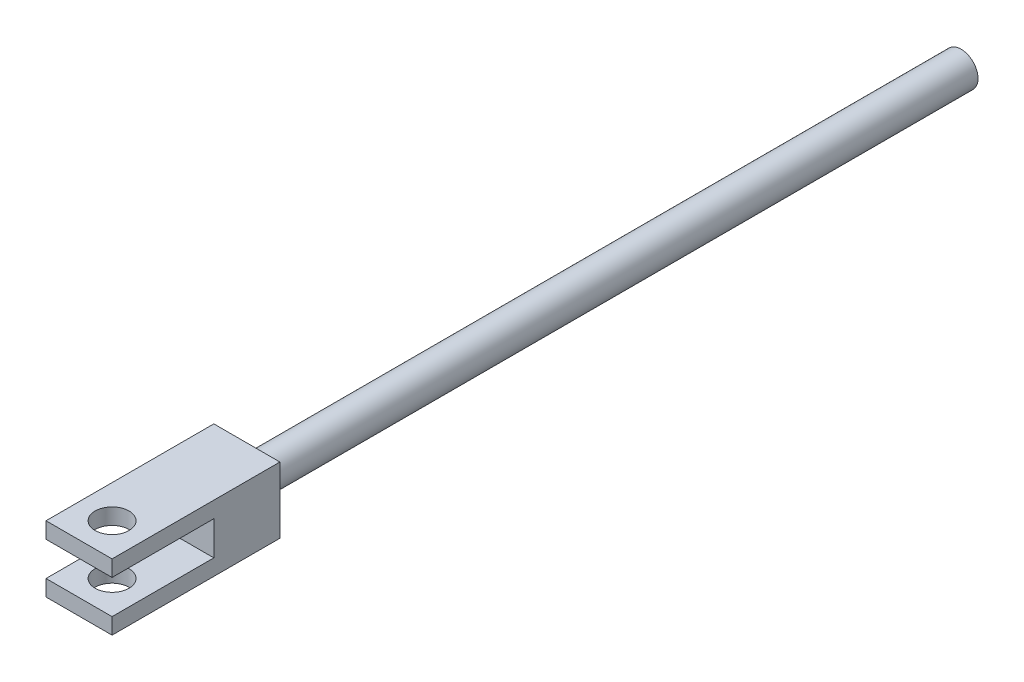
SolidWorks part; units mm, degrees
material "6061-T6 (SS)"
ref_plane "Front Plane" through (0, 0, 0) normal (0, 0, 1) x (1, 0, 0)
ref_plane "Top Plane" through (0, 0, 0) normal (0, 1, 0) x (1, 0, 0)
ref_plane "Right Plane" through (0, 0, 0) normal (1, 0, 0) x (0, 0, -1)
sketch "Sketch1" plane through (0, 0, 0) normal (0, 0, 1) x (1, 0, 0)
  line L1 (-4.699, 4.699) -> (4.699, 4.699)
  line L2 (-4.699, 4.699) -> (-4.699, -4.699)
  line L3 (-4.699, -4.699) -> (4.699, -4.699)
  line L4 (4.699, 4.699) -> (4.699, -4.699)
  line L5 (-4.699, 4.699) -> (4.699, -4.699) construction
  line L6 (-4.699, -4.699) -> (4.699, 4.699) construction
  point P0 (0, 0)
  dimension "D1" = 9.398
extrude "Boss-Extrude1" add sketch "Sketch1" along normal blind 23.876
sketch "Sketch2" plane through (4.699, 0, 0) normal (1, 0, 0) x (0, 0, -1)
  line L0 (-23.876, -4.699) -> (-23.876, 4.699) construction
  line L1 (-23.876, 2.413) -> (-9.398, 2.413)
  line L2 (-23.876, 2.413) -> (-23.876, -2.413)
  line L3 (-23.876, -2.413) -> (-9.398, -2.413)
  line L4 (-9.398, 2.413) -> (-9.398, -2.413)
  line L5 (-9.398, 2.413) -> (-9.398, 4.699) construction
  line L6 (-23.876, 4.699) -> (0, 4.699) construction
  line L7 (-9.398, -2.413) -> (-9.398, -4.699) construction
  line L8 (-23.876, -4.699) -> (0, -4.699) construction
  dimension "D1" = 14.478
  dimension "D2" = 4.826
extrude "Cut-Extrude1" cut sketch "Sketch2" against normal through all
sketch "Sketch3" plane through (0, 4.699, 0) normal (0, 1, 0) x (1, 0, 0)
  line L0 (0, -23.876) -> (0, -19.177) construction
  line L1 (4.699, -23.876) -> (-4.699, -23.876) construction
  line L2 (0, -19.177) -> (4.699, -19.177) construction
  line L3 (4.699, -23.876) -> (4.699, 0) construction
  circle A0 centre (0, -19.177) radius 2.413
  dimension "D1" = 4.826
extrude "Cut-Extrude2" cut sketch "Sketch3" against normal through all
sketch "Sketch4" plane through (0, 0, 0) normal (0, 0, -1) x (-1, 0, 0)
  circle A0 centre (0, 0) radius 2.413
  dimension "D1" = 4.826
extrude "Boss-Extrude2" add sketch "Sketch4" along normal blind 101.6
